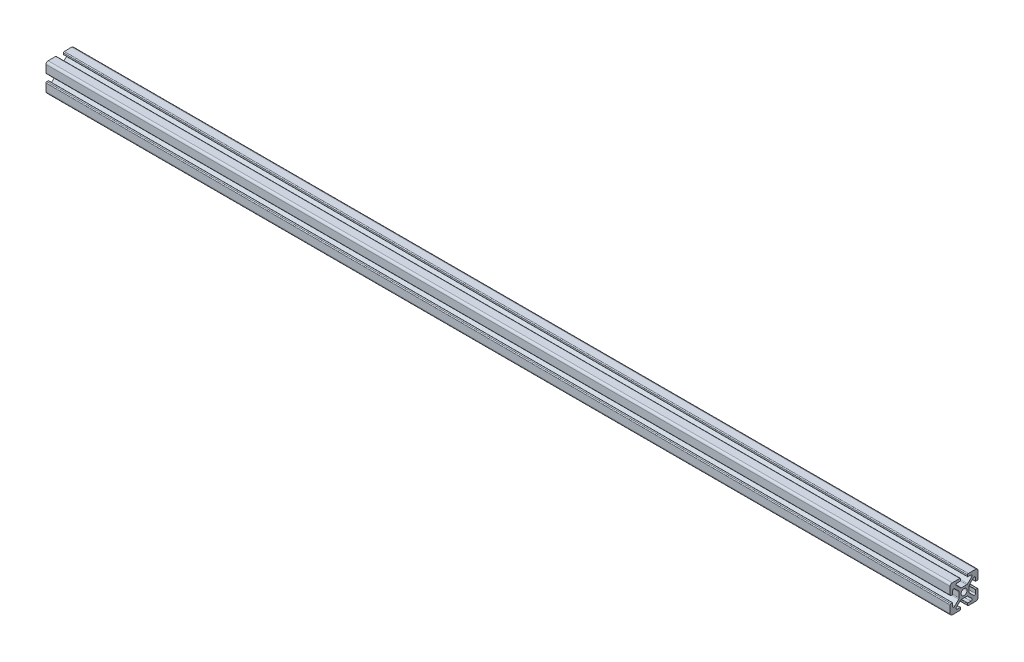
SolidWorks part; units mm, degrees
ref_plane "Front Plane" through (0, 0, 0) normal (0, 0, 1) x (1, 0, 0)
ref_plane "Top Plane" through (0, 0, 0) normal (0, 1, 0) x (1, 0, 0)
ref_plane "Right Plane" through (0, 0, 0) normal (1, 0, 0) x (0, 0, -1)
sketch "Sketch1" plane through (0, 0, 0) normal (1, 0, 0) x (0, 0, -1)
  line L0 (0, -10) -> (0, 10) construction
  line L1 (10, -10) -> (-10, -10)
  line L2 (10, -10) -> (10, 10)
  line L3 (10, 10) -> (0, 10)
  line L4 (-10, -10) -> (-10, 10)
  line L5 (10, -10) -> (-10, 10) construction
  line L6 (10, 10) -> (-10, -10) construction
  line L7 (10, 0) -> (-10, 0) construction
  line L8 (-2.5, 9.4) -> (-2.5, 8.3731)
  line L9 (-2.7, 8.1731) -> (-4.95, 8.1731)
  line L10 (-5.5157, 6.8075) -> (-2.6011, 3.8929)
  line L11 (-1.894, 3.6) -> (0, 3.6)
  line L12 (-5.3502, 4.0584) -> (-4.0584, 5.3502) construction
  line L13 (-3.825, 8.1731) -> (-3.825, 10) construction
  line L14 (-3.1, 10) -> (-10, 10)
  line L15 (-5.75, 7.3731) -> (5.75, 7.3731) construction
  circle A0 centre (0, 0) radius 2.15
  arc A1 (-4.95, 8.1731) -> (-5.5157, 6.8075) centre (-4.95, 7.3731) ccw
  arc A2 (-2.6011, 3.8929) -> (-1.894, 3.6) centre (-1.894, 4.6) ccw
  arc A3 (-2.5, 8.3731) -> (-2.7, 8.1731) centre (-2.7, 8.3731) cw
  arc A4 (-2.5, 9.4) -> (-3.1, 10) centre (-3.1, 9.4) ccw
  point P0 (0, 0)
  point P9 (0, 0)
  point P12 (0, 0)
  point P22 (-4.7043, 4.7043)
  point P32 (-2.5, 10)
  point P33 (-2.5, 8.8866)
  point P35 (-4.0584, 5.3502)
  point P37 (0, 7.3731)
  dimension "Center Hole Diameter" = 4.3
  dimension "D4" = 1
  dimension "D5" = 0.2
  dimension "D6" = 0.6
  dimension "D3" = 0.8
  dimension "Rail Height" = 20
  dimension "D7" = 6.4
  dimension "T Slot Width" = 5
  dimension "D10" = 10
  dimension "Rail Width" = 20
  dimension "D2" = 11.5
sketch "Sketch2" plane through (0, 0, 0) normal (0, 0, 1) x (1, 0, 0)
  line L0 (-132.4, 10) -> (-132.4, -10) construction
  line L1 (152.4, -10) -> (-152.4, -10) construction
  line L2 (152.4, -10) -> (152.4, 10) construction
  line L3 (152.4, 10) -> (-152.4, 10) construction
  line L4 (-152.4, -10) -> (-152.4, 10) construction
  line L5 (152.4, -10) -> (-152.4, 10) construction
  line L6 (152.4, 10) -> (-152.4, -10) construction
  line L7 (132.4, 10) -> (132.4, -10) construction
  point P0 (0, 0)
  point P12 (132.4, 0)
  dimension "Length" = 304.8
  dimension "D1" = 20
  dimension "D2" = 20
sketch "Sketch3" plane through (0, 0, 0) normal (1, 0, 0) x (0, 0, -1)
  line L0 (-5.5157, 6.8075) -> (-2.6011, 3.8929) construction
  line L5 (-3.1, 10) -> (-10, 10) construction
  line L6 (-2.5, 9.4) -> (-2.5, 8.3731) construction
  line L7 (-2.7, 8.1731) -> (-4.95, 8.1731) construction
  line L8 (-1.894, 3.6) -> (0, 3.6) construction
  line L9 (-5.5157, 6.8075) -> (-2.6011, 3.8929)
  line L10 (-10, 10) -> (0, 0) construction
  line L12 (-3.6, 1.894) -> (-3.6, 0)
  line L13 (-8.1731, 2.7) -> (-8.1731, 4.95)
  line L14 (-3.1, 10) -> (-8.5, 10)
  line L15 (-2.5, 9.4) -> (-2.5, 8.3731)
  line L16 (-2.7, 8.1731) -> (-4.95, 8.1731)
  line L17 (-1.894, 3.6) -> (0, 3.6)
  line L18 (-9.4, 2.5) -> (-8.3731, 2.5)
  line L19 (-10, 3.1) -> (-10, 8.5)
  line L20 (-6.8075, 5.5157) -> (-3.8929, 2.6011)
  line L21 (-3.6, 0) -> (-2.15, 0)
  line L22 (0, 3.6) -> (0, 2.15)
  arc A0 (-2.5, 9.4) -> (-3.1, 10) centre (-3.1, 9.4) ccw construction
  arc A1 (-2.7, 8.1731) -> (-2.5, 8.3731) centre (-2.7, 8.3731) ccw construction
  arc A2 (-4.95, 8.1731) -> (-5.5157, 6.8075) centre (-4.95, 7.3731) ccw construction
  arc A3 (-2.6011, 3.8929) -> (-1.894, 3.6) centre (-1.894, 4.6) ccw construction
  arc A4 (-2.5, 9.4) -> (-3.1, 10) centre (-3.1, 9.4) ccw
  arc A5 (-2.7, 8.1731) -> (-2.5, 8.3731) centre (-2.7, 8.3731) ccw
  arc A6 (-4.95, 8.1731) -> (-5.5157, 6.8075) centre (-4.95, 7.3731) ccw
  arc A7 (-2.6011, 3.8929) -> (-1.894, 3.6) centre (-1.894, 4.6) ccw
  arc A8 (-3.8929, 2.6011) -> (-3.6, 1.894) centre (-4.6, 1.894) cw
  arc A9 (-8.1731, 4.95) -> (-6.8075, 5.5157) centre (-7.3731, 4.95) cw
  arc A10 (-8.1731, 2.7) -> (-8.3731, 2.5) centre (-8.3731, 2.7) cw
  arc A11 (-9.4, 2.5) -> (-10, 3.1) centre (-9.4, 3.1) cw
  circle A12 centre (0, 0) radius 2.15 construction
  arc A13 (0, 2.15) -> (-2.15, 0) centre (0, 0) ccw
  arc A14 (-10, 8.5) -> (-8.5, 10) centre (-8.5, 8.5) cw
  dimension "D1" = 1.5
extrude "Boss-Extrude1" add sketch "Sketch3" against normal blind 650
mirror "Mirror1" about plane through (0, 0, 0) normal (0, 1, 0) of bodies 104
mirror "Mirror2" about plane through (0, 0, 0) normal (0, 0, 1) of bodies 105
equation "\"D10@Sketch1\" = \"Rail Height@Sketch1\" / 2"
equation "\"D2@Sketch2\"=\"D1@Sketch2\""
